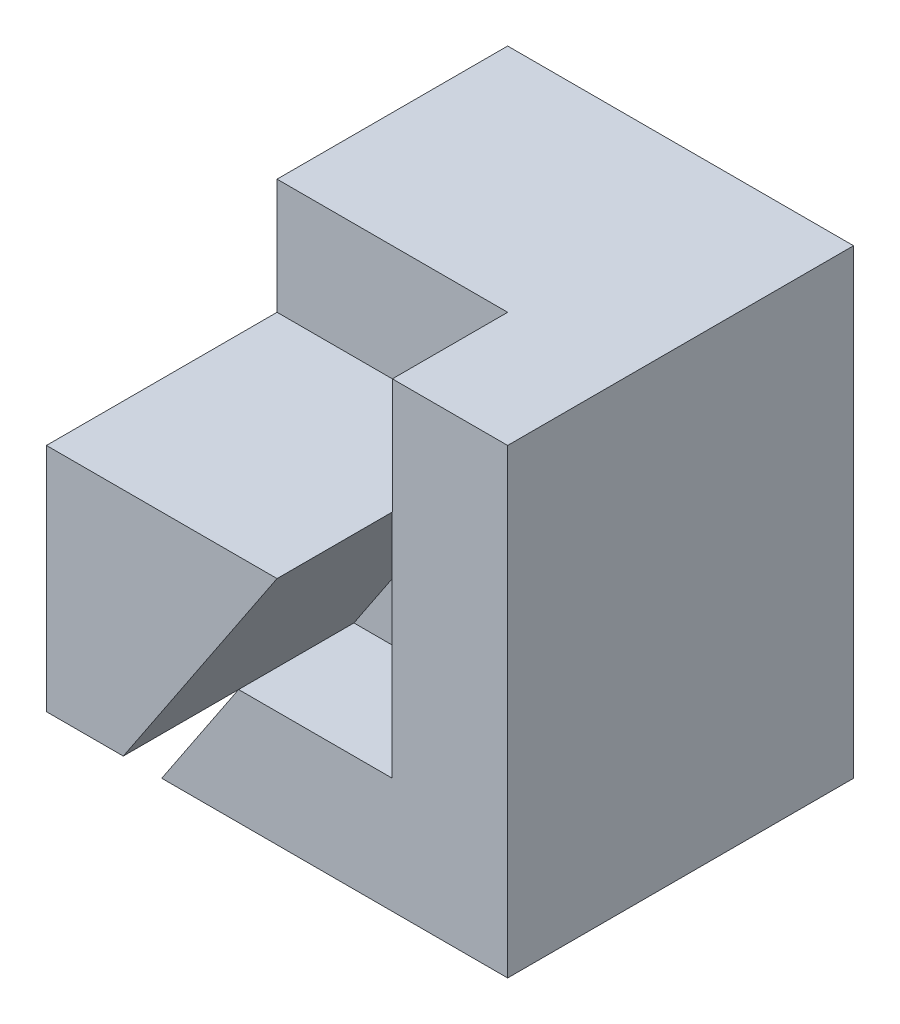
SolidWorks part; units mm, degrees
ref_plane "Front Plane" through (0, 0, 0) normal (0, 0, 1) x (1, 0, 0)
ref_plane "Top Plane" through (0, 0, 0) normal (0, 1, 0) x (1, 0, 0)
ref_plane "Right Plane" through (0, 0, 0) normal (1, 0, 0) x (0, 0, -1)
sketch "Sketch1" plane through (0, 0, 0) normal (0, 0, 1) x (1, 0, 0)
  line L1 (0, 0) -> (40, 0)
  line L2 (0, 0) -> (0, 40)
  line L3 (0, 40) -> (40, 40)
  line L4 (40, 0) -> (40, 40)
  dimension "D1" = 40
  dimension "D2" = 40
extrude "Boss-Extrude1" add sketch "Sketch1" along normal blind 40
sketch "Sketch2" plane through (0, 0, 40) normal (0, 0, 1) x (1, 0, 0)
  line L1 (0, 40) -> (10, 40)
  line L2 (0, 40) -> (0, 30)
  line L3 (0, 30) -> (10, 30)
  line L4 (10, 40) -> (10, 30)
  dimension "D1" = 10
  dimension "D2" = 10
extrude "Cut-Extrude1" cut sketch "Sketch2" against normal blind 40
sketch "Sketch4" plane through (0, 40, 0) normal (0, 1, 0) x (1, 0, 0)
  line L1 (40, -40) -> (30, -40)
  line L2 (40, -40) -> (40, -30)
  line L3 (40, -30) -> (30, -30)
  line L4 (30, -40) -> (30, -30)
  line L5 (10, -40) -> (0, -40)
  line L6 (10, -40) -> (10, -10)
  line L7 (10, -10) -> (0, -10)
  line L8 (0, -40) -> (0, -10)
  dimension "D1" = 10
  dimension "D2" = 10
  dimension "D3" = 10
  dimension "D4" = 30
extrude "Cut-Extrude2" cut sketch "Sketch4" against normal blind 40
sketch "Sketch5" plane through (0, 0, 40) normal (0, 0, 1) x (1, 0, 0)
  line L0 (10, 0) -> (10, 40) construction
  line L1 (30, 0) -> (10, 0)
  line L2 (30, 0) -> (30, 10)
  line L3 (30, 10) -> (10, 10)
  line L4 (10, 0) -> (10, 10)
  dimension "D1" = 10
extrude "Cut-Extrude3" cut sketch "Sketch5" against normal blind 10
sketch "Sketch7" plane through (0, 0, 40) normal (0, 0, 1) x (1, 0, 0)
  line L0 (10, 10) -> (10, 40) construction
  line L1 (30, 40) -> (10, 40)
  line L2 (30, 40) -> (30, 30)
  line L3 (30, 30) -> (10, 30)
  line L4 (10, 40) -> (10, 30)
  dimension "D1" = 10
extrude "Cut-Extrude16" cut sketch "Sketch7" against normal blind 20
sketch "Sketch11" plane through (0, 0, 40) normal (0, 0, 1) x (1, 0, 0)
  line L1 (10, 30) -> (30, 30)
  line L2 (10, 30) -> (10, 10)
  line L3 (10, 10) -> (30, 10)
  line L4 (30, 30) -> (30, 10)
extrude "Cut-Extrude19" cut sketch "Sketch11" against normal blind 10
sketch "Sketch12" plane through (0, 0, 0) normal (0, 0, -1) x (-1, 0, 0)
  line L0 (-10, 30) -> (-40, 40)
  line L1 (-40, 40) -> (-10, 40)
  line L2 (-10, 40) -> (-10, 30)
extrude "Cut-Extrude20" cut sketch "Sketch12" against normal blind 10
sketch "Sketch13" plane through (0, 0, 20) normal (0, 0, 1) x (1, 0, 0)
  line L1 (10, 40) -> (30, 40)
  line L2 (10, 40) -> (10, 30)
  line L3 (10, 30) -> (30, 30)
  line L4 (30, 40) -> (30, 30)
extrude "Cut-Extrude21" cut sketch "Sketch13" against normal blind 10
ref_plane "Plane1" through (30, 30, 30) normal (0, 1, 0) x (1, 0, 0)
sketch "Sketch15" plane through (0, 0, 0) normal (0, 0, -1) x (-1, 0, 0)
  line L0 (-40, 40) -> (-10, 40)
  line L1 (-10, 30) -> (-10, 40)
  line L2 (-40, 40) -> (-10, 30)
extrude "Boss-Extrude2" add sketch "Sketch15" against normal blind 10
sketch "Sketch16" plane through (0, 0, 30) normal (0, 0, 1) x (1, 0, 0)
  line L1 (10, 30) -> (30, 30)
  line L2 (10, 30) -> (10, 10)
  line L3 (10, 10) -> (30, 10)
  line L4 (30, 30) -> (30, 10)
  dimension "D1" = 20
  dimension "D2" = 20
extrude "Cut-Extrude25" cut sketch "Sketch16" against normal blind 10
sketch "Sketch19" plane through (0, 0, 30) normal (0, 0, 1) x (1, 0, 0)
  line L0 (10, 0) -> (30, 30)
  line L1 (30, 30) -> (10, 30)
  line L2 (10, 30) -> (10, 0)
  dimension "D1" = 20
  dimension "D2" = 30
extrude "Cut-Extrude26" cut sketch "Sketch19" against normal blind 10
sketch "Sketch22" plane through (0, 0, 10) normal (0, 0, 1) x (1, 0, 0)
  line L1 (10, 40) -> (30, 40)
  line L2 (10, 40) -> (10, 30)
  line L3 (10, 30) -> (30, 30)
  line L4 (30, 40) -> (30, 30)
extrude "Boss-Extrude5" add sketch "Sketch22" along normal blind 10
sketch "Sketch23" plane through (0, 0, 20) normal (0, 0, 1) x (1, 0, 0)
  line L0 (16.6667, 10) -> (10, 10)
  line L1 (10, 40) -> (10, 0) construction
  line L2 (10, 10) -> (10, 0)
  line L3 (10, 0) -> (16.6667, 10)
extrude "Boss-Extrude6" add sketch "Sketch23" along normal blind 10
sketch "Sketch24" plane through (0, 0, 20) normal (0, 0, 1) x (1, 0, 0)
  line L0 (30, 10) -> (30, 40) construction
  line L1 (10, 10) -> (30, 10)
  line L2 (10, 10) -> (10, 30)
  line L3 (10, 30) -> (30, 30)
  line L4 (30, 10) -> (30, 30)
  dimension "D1" = 20
extrude "Boss-Extrude7" add sketch "Sketch24" along normal blind 10
sketch "Sketch25" plane through (0, 0, 30) normal (0, 0, 1) x (1, 0, 0)
  line L0 (10, 0) -> (30, 30)
  line L1 (30, 30) -> (10, 30)
  line L2 (10, 30) -> (10, 0)
extrude "Boss-Extrude8" add sketch "Sketch25" along normal blind 10
sketch "Sketch26" plane through (0, 0, 30) normal (0, 0, 1) x (1, 0, 0)
  line L0 (30, 30) -> (30, 10)
  line L1 (30, 10) -> (16.6667, 10)
  line L2 (10, 0) -> (30, 30) construction
  line L3 (30, 30) -> (16.6667, 10)
  dimension "D1" = 20
extrude "Boss-Extrude9" add sketch "Sketch26" along normal blind 10
sketch "Sketch27" plane through (0, 0, 40) normal (0, 0, 1) x (1, 0, 0)
  line L0 (10, 0) -> (30, 30)
  line L1 (30, 30) -> (10, 30)
  line L2 (10, 30) -> (10, 0)
extrude "Cut-Extrude27" cut sketch "Sketch27" against normal blind 10
sketch "Sketch28" plane through (0, 0, 30) normal (0, 0, 1) x (1, 0, 0)
  line L0 (16.6667, 10) -> (10, 0)
  line L1 (10, 0) -> (16.6667, 10)
  line L2 (16.6667, 10) -> (10, 10)
  line L3 (10, 30) -> (10, 0) construction
  line L4 (10, 10) -> (10, 0)
  line L5 (10, 10) -> (10, 30)
  line L6 (10, 30) -> (30, 30)
  line L7 (30, 30) -> (16.6667, 10)
  line M2 (16.6667, 10) -> (30, 30)
  line M3 (30, 30) -> (10, 30)
  line M4 (10, 30) -> (10, 0)
extrude "Boss-Extrude12" add sketch "Sketch28" along normal blind 10 contours L2 M2 M3 M4 | L0 L2 M4
sketch "Sketch29" plane through (0, 0, 40) normal (0, 0, 1) x (1, 0, 0)
  line L0 (16.6667, 10) -> (30, 30)
  line L1 (16.6667, 10) -> (29.9667, 10)
  line L2 (16.6667, 10) -> (30, 10) construction
  line L3 (29.9667, 10) -> (29.9667, 29.95)
  line M5 (16.6667, 10) -> (30, 10)
  dimension "D1" = 13.3
extrude "Cut-Extrude30" cut sketch "Sketch29" against normal blind 20 contours L3 L0 M5
sketch "Sketch30" plane through (0, 0, 40) normal (0, 0, 1) x (1, 0, 0)
  line L0 (30, 30) -> (10, 30)
  line L1 (10, 30) -> (10, 10)
  line L2 (10, 30) -> (10, 0) construction
  line L3 (10, 10) -> (16.6667, 10)
  line L4 (10, 0) -> (29.9667, 29.95) construction
  line L5 (16.6667, 10) -> (30, 30)
  dimension "D1" = 20
extrude "Cut-Extrude31" cut sketch "Sketch30" against normal blind 10
sketch "Sketch32" plane through (29.9667, 0, 0) normal (-1, 0, 0) x (0, 0, 1)
  line L1 (30, 29.95) -> (40, 29.95)
  line L2 (30, 29.95) -> (30, 10)
  line L3 (30, 10) -> (40, 10)
  line L4 (40, 29.95) -> (40, 10)
extrude "Cut-Extrude36" cut sketch "Sketch32" against normal blind 10
sketch "Sketch33" plane through (0, 29.95, 0) normal (0, -1, 0) x (1, 0, 0)
  line L1 (29.9667, 30) -> (30, 30)
  line L2 (29.9667, 30) -> (29.9667, 40)
  line L3 (29.9667, 40) -> (30, 40)
  line L4 (30, 30) -> (30, 40)
extrude "Cut-Extrude37" cut sketch "Sketch33" against normal blind 10
sketch "Sketch34" plane through (0, 0, 30) normal (0, 0, 1) x (1, 0, 0)
  line L0 (10, 10) -> (16.6667, 10)
  line L1 (16.6667, 10) -> (30, 30)
  line L2 (30, 30) -> (10, 30)
  line L3 (10, 30) -> (10, 10)
extrude "Boss-Extrude13" add sketch "Sketch34" along normal blind 10
sketch "Sketch35" plane through (0, 0, 40) normal (0, 0, 1) x (1, 0, 0)
  line L0 (10, 0) -> (10, 9.999)
  line L3 (10, 30) -> (10, 0) construction
  line L4 (10, 9.999) -> (16.666, 9.999)
  line L5 (10, 0) -> (30, 30) construction
  line L6 (16.666, 9.999) -> (10, 0)
  dimension "D1" = 9.999
extrude "Cut-Extrude40" cut sketch "Sketch35" against normal blind 20
